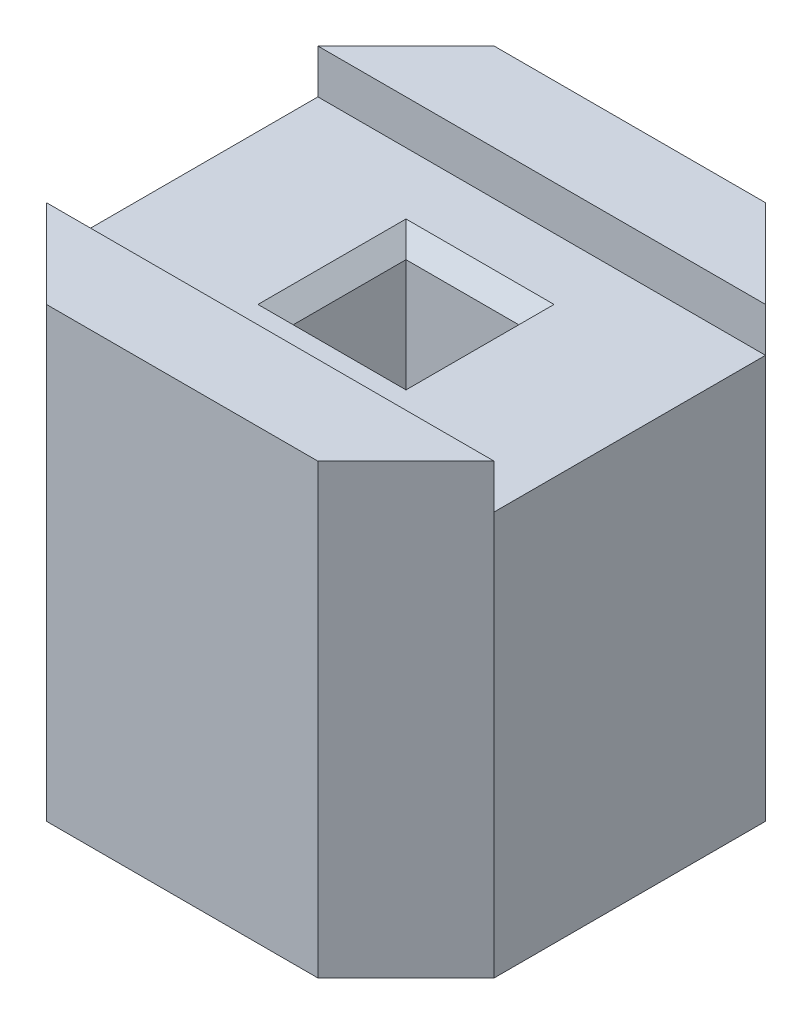
SolidWorks part; units mm, degrees
ref_plane "Front Plane" through (0, 0, 0) normal (0, 0, 1) x (1, 0, 0)
ref_plane "Top Plane" through (0, 0, 0) normal (0, 1, 0) x (1, 0, 0)
ref_plane "Right Plane" through (0, 0, 0) normal (1, 0, 0) x (0, 0, -1)
sketch "Sketch1" plane through (0, 0, 0) normal (0, 0, 1) x (1, 0, 0)
  line L1 (0, 0) -> (2.54, 0)
  line L2 (0, 0) -> (0, -2.54)
  line L3 (0, -2.54) -> (2.54, -2.54)
  line L4 (2.54, 0) -> (2.54, -2.54)
  dimension "D1" = 2.54
  dimension "D2" = 2.54
extrude "Boss-Extrude1" add sketch "Sketch1" along normal blind 2.54
chamfer "Chamfer1" distance 0.5 angle 45 4 edges at (0, -1.27, 2.54) (0, -1.27, 0) (2.54, -1.27, 0) (2.54, -1.27, 2.54)
sketch "Sketch2" plane through (0, 0, 0) normal (0, 1, 0) x (1, 0, 0)
  line L0 (0, -1.27) -> (3.6898, -1.27) construction
  line L1 (0, -0.5) -> (2.54, -0.5)
  line L2 (0, -0.5) -> (0, -2.04)
  line L3 (0, -2.04) -> (2.54, -2.04)
  line L4 (2.54, -0.5) -> (2.54, -2.04)
  line L5 (2.04, 0) -> (0.5, 0) construction
  dimension "D1" = 1.54
  dimension "D2" = 1.27
  dimension "D3" = 0.77
  dimension "D4" = 2.54
extrude "Cut-Extrude6" cut sketch "Sketch2" against normal blind 0.25 contours L1 L4 L3 L2
sketch "Sketch3" plane through (0, -0.25, 0) normal (0, 1, 0) x (1, 0, 0)
  line L3 (0.95, -0.95) -> (1.59, -0.95)
  line L4 (0.95, -0.95) -> (0.95, -1.59)
  line L5 (0.95, -1.59) -> (1.59, -1.59)
  line L6 (1.59, -0.95) -> (1.59, -1.59)
  line L7 (0.95, -0.95) -> (1.59, -1.59) construction
  line L8 (0.95, -1.59) -> (1.59, -0.95) construction
  line L13 (2.04, 0) -> (0.5, 0) construction
  line L14 (2.54, -0.5) -> (2.54, -2.04) construction
  point P2 (1.27, -1.27)
  dimension "D1" = 1.27
  dimension "D2" = 1.27
  dimension "D4" = 0.64
  dimension "D5" = 0.64
extrude "Cut-Extrude7" cut sketch "Sketch3" against normal blind 3
chamfer "Chamfer4" distance 0.1 angle 45 4 edges at (1.27, -0.25, 1.59) (1.59, -0.25, 1.27) (0.95, -0.25, 1.27) (1.27, -0.25, 0.95)
